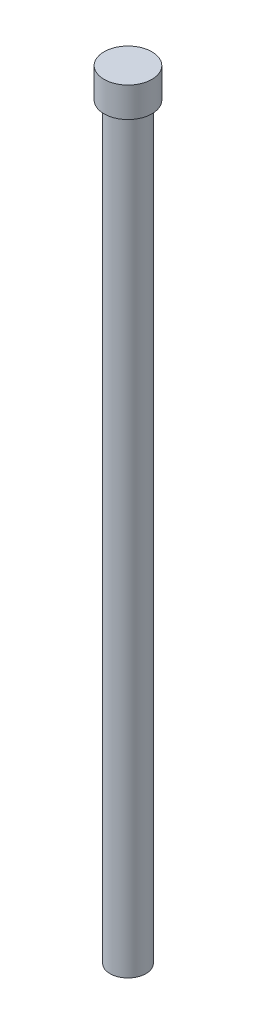
SolidWorks part; units mm, degrees
material "Stainless Steel (ferritic)"
ref_plane "Front Plane" through (0, 0, 0) normal (0, 0, 1) x (1, 0, 0)
ref_plane "Top Plane" through (0, 0, 0) normal (0, 1, 0) x (1, 0, 0)
ref_plane "Right Plane" through (0, 0, 0) normal (1, 0, 0) x (0, 0, -1)
sketch "Sketch1" plane through (0, 0, 0) normal (0, 1, 0) x (1, 0, 0)
  circle A0 centre (0, 0) radius 0.762
  dimension "D1" = 1.524
extrude "Boss-Extrude1" add sketch "Sketch1" along normal blind 31.75
sketch "Sketch2" plane through (0, 31.75, 0) normal (0, 1, 0) x (1, 0, 0)
  circle A0 centre (0, 0) radius 1.016
extrude "Boss-Extrude2" add sketch "Sketch2" along normal blind 1.27
